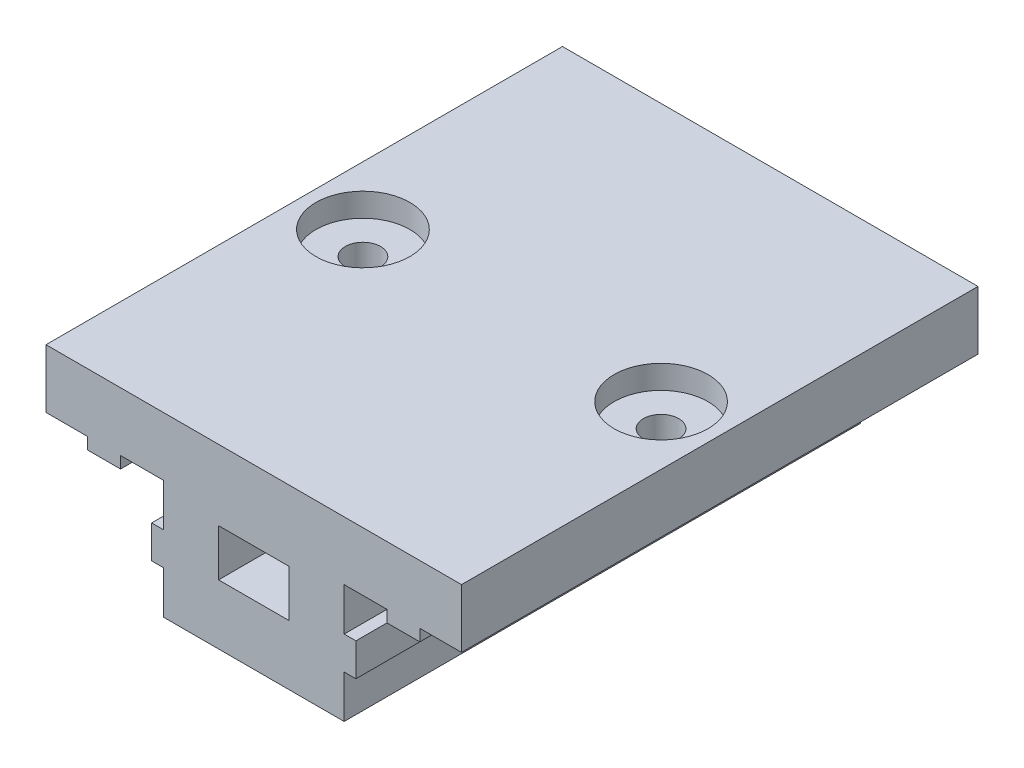
SolidWorks part; units mm, degrees
ref_plane "Front Plane" through (0, 0, 0) normal (0, 0, 1) x (1, 0, 0)
ref_plane "Top Plane" through (0, 0, 0) normal (0, 1, 0) x (1, 0, 0)
ref_plane "Right Plane" through (0, 0, 0) normal (1, 0, 0) x (0, 0, -1)
sketch "Esquisse1" plane through (0, 0, 0) normal (0, 0, 1) x (1, 0, 0)
  line L0 (0, 15.1) -> (17.7, 15.1)
  line L1 (17.7, 15.1) -> (17.7, 10.1)
  line L2 (17.7, 10.1) -> (14.15, 10.1)
  line L3 (14.15, 10.1) -> (14.15, 9.1)
  line L4 (14.15, 9.1) -> (11.35, 9.1)
  line L5 (11.35, 9.1) -> (11.35, 10.1)
  line L6 (11.35, 10.1) -> (7.7, 10.1)
  line L7 (7.7, 10.1) -> (7.7, 6.45)
  line L8 (7.7, 6.45) -> (8.7, 6.45)
  line L9 (8.7, 6.45) -> (8.7, 3.65)
  line L10 (8.7, 3.65) -> (7.7, 3.65)
  line L11 (7.7, 3.65) -> (7.7, 0)
  line L12 (7.7, 0) -> (0, 0)
  line L15 (0, 0) -> (0, 15.1)
  point P0 (1.5992, 16.9737)
  dimension "D1" = 17.7
  dimension "D2" = 10
  dimension "D4" = 1
  dimension "D5" = 2.8
  dimension "D6" = 5
  dimension "D7" = 3.55
extrude "Boss.-Extru.1" add sketch "Esquisse1" along normal blind 44
sketch "Esquisse3" plane through (0, 15.1, 0) normal (0, 1, 0) x (1, 0, 0)
  line L0 (17.7, -44) -> (17.7, 0) construction
  circle A0 centre (12.7, -22) radius 1.5
  point P6 (17.7, -22)
  dimension "D2" = 3
  dimension "D1" = 5
extrude "Enlèv. mat.-Extru.2" cut sketch "Esquisse3" against normal through all
sketch "Esquisse4" plane through (0, 15.1, 0) normal (0, 1, 0) x (1, 0, 0)
  circle A0 centre (12.7, -22) radius 4
  circle A1 centre (12.7, -22) radius 1.5 construction
  dimension "D1" = 8
extrude "Enlèv. mat.-Extru.3" cut sketch "Esquisse4" against normal blind 2
mirror "Symétrie1" about plane through (0, 0, 44) normal (1, 0, 0) of bodies 105 101
sketch "Esquisse5" plane through (0, 0, 44) normal (0, 0, 1) x (1, 0, 0)
  line L0 (8.7, 3.65) -> (8.7, 6.45) construction
  line L1 (-3, 9.1) -> (3, 9.1)
  line L2 (-3, 9.1) -> (-3, 5.1)
  line L3 (-3, 5.1) -> (3, 5.1)
  line L4 (3, 9.1) -> (3, 5.1)
  line L5 (17.7, 15.1) -> (-17.7, 15.1) construction
  point P7 (8.7, 5.05)
  point P8 (0, 5.1)
  dimension "D1" = 6
  dimension "D2" = 4
  dimension "D3" = 6
extrude "Enlèv. mat.-Extru.4" cut sketch "Esquisse5" against normal through all
